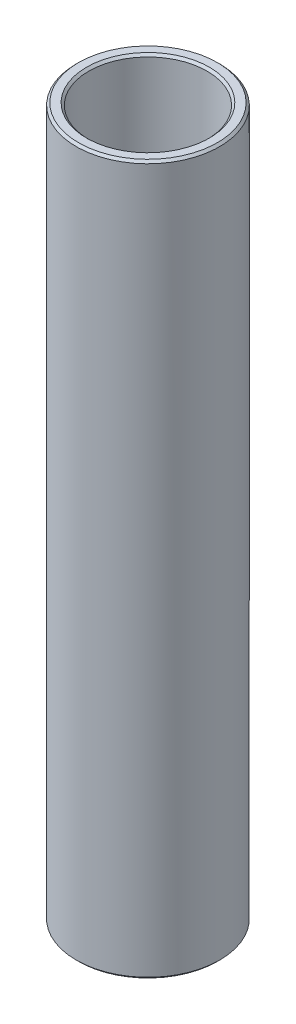
SolidWorks part; units mm, degrees
ref_plane "Front Plane" through (0, 0, 0) normal (0, 0, 1) x (1, 0, 0)
ref_plane "Top Plane" through (0, 0, 0) normal (0, 1, 0) x (1, 0, 0)
ref_plane "Right Plane" through (0, 0, 0) normal (1, 0, 0) x (0, 0, -1)
sketch "Sketch1" plane through (0, 0, 0) normal (0, 0, 1) x (1, 0, 0)
  line L0 (0, 19.775) -> (0, -19.775) construction
  line L1 (-3.3, 19.775) -> (-4, 19.775)
  line L2 (-4, 19.775) -> (-4, -19.775)
  line L3 (-4, -19.775) -> (-3.3, -19.775)
  line L4 (-3.3, -19.775) -> (-3.3, 19.775)
  point P1 (-3.3, 0)
  dimension "D1" = 39.55
  dimension "D2" = 8
  dimension "D3" = 6.6
revolve "Revolve1" add sketch "Sketch1" angle 360 about L0
chamfer "Chamfer1" distance 0.127 angle 45 4 edges at (-4, -19.775, 0) (-3.3, -19.775, 0) (-3.3, 19.775, 0) (-4, 19.775, 0)
